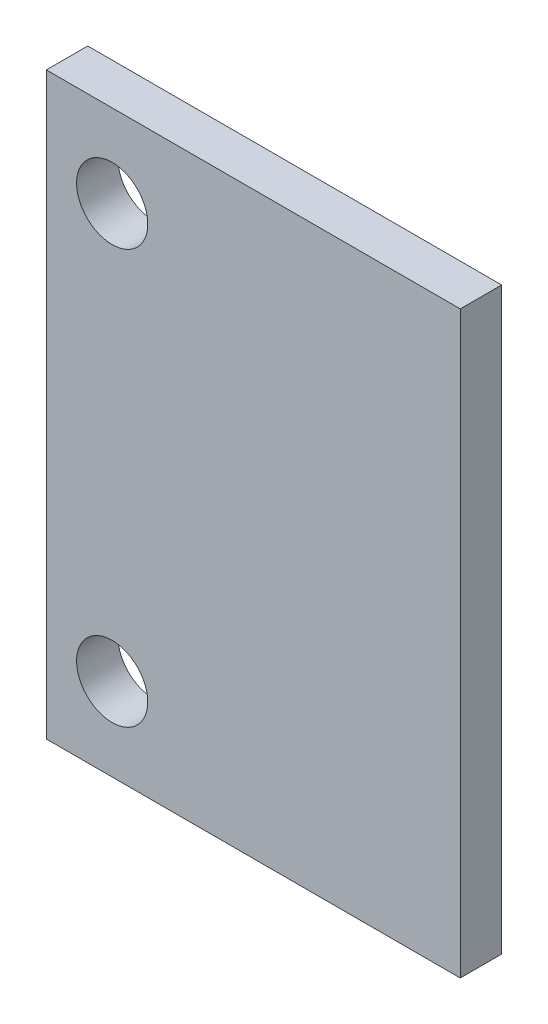
SolidWorks part; units mm, degrees
ref_plane "Front Plane" through (0, 0, 0) normal (0, 0, 1) x (1, 0, 0)
ref_plane "Top Plane" through (0, 0, 0) normal (0, 1, 0) x (1, 0, 0)
ref_plane "Right Plane" through (0, 0, 0) normal (1, 0, 0) x (0, 0, -1)
sketch "Sketch1" plane through (0, 0, 0) normal (0, 0, 1) x (1, 0, 0)
  line L0 (-4.3307, 6.35) -> (-4.3307, -6.35) construction
  line L1 (-6.35, -8.89) -> (6.35, -8.89)
  line L2 (-6.35, -8.89) -> (-6.35, 8.89)
  line L3 (-6.35, 8.89) -> (6.35, 8.89)
  line L4 (6.35, -8.89) -> (6.35, 8.89)
  circle A0 centre (-4.3307, 6.35) radius 1.0922
  circle A1 centre (-4.3307, -6.35) radius 1.0922
  point P0 (0, 0)
  point P10 (-4.3307, 0)
  point P11 (-6.35, 0)
  point P12 (0, 8.89)
  dimension "D4" = 2.1844
  dimension "D1" = 12.7
  dimension "D2" = 17.78
  dimension "D3" = 12.7
  dimension "D5" = 4.3307
extrude "Boss-Extrude1" add sketch "Sketch1" along normal mid plane 1.27
